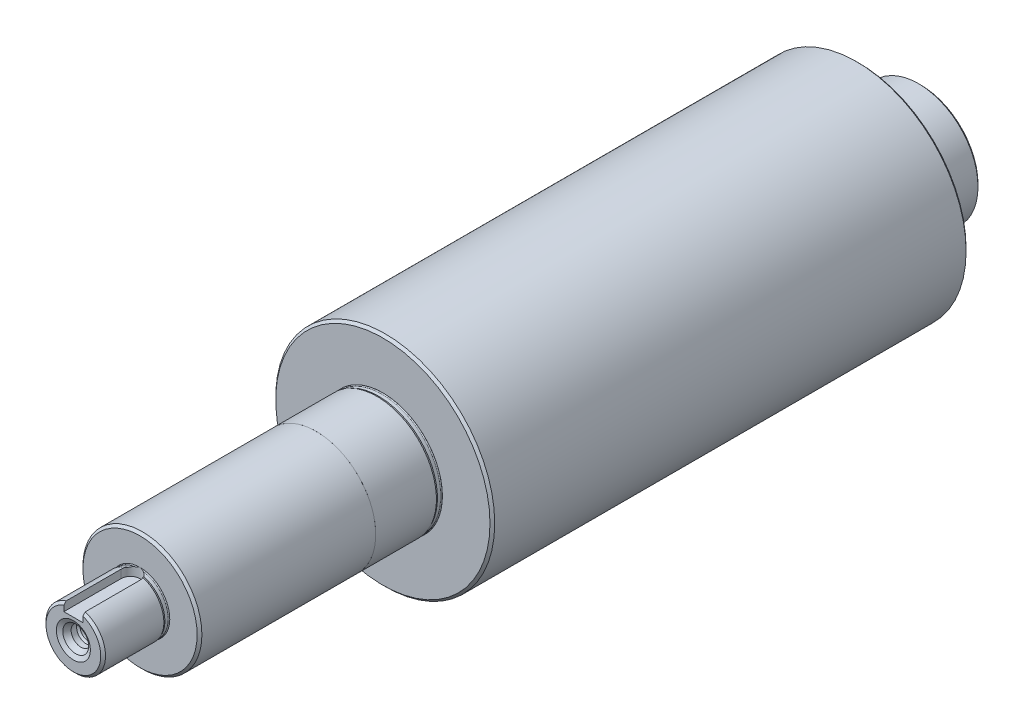
SolidWorks part; units mm, degrees
ref_plane "Přední rovina" through (0, 0, 0) normal (0, 0, 1) x (1, 0, 0)
ref_plane "Horní rovina" through (0, 0, 0) normal (0, 1, 0) x (1, 0, 0)
ref_plane "Pravá rovina" through (0, 0, 0) normal (1, 0, 0) x (0, 0, -1)
sketch "Skica1" plane through (0, 0, 0) normal (0, 0, 1) x (1, 0, 0)
  circle A0 centre (0, 0) radius 25
  dimension "D1" = 50
extrude "Přidat vysunutím1" add sketch "Skica1" along normal blind 26
sketch "Skica2" plane through (0, 0, 26) normal (0, 0, 1) x (1, 0, 0)
  circle A0 centre (0, 0) radius 46
  dimension "D1" = 92
extrude "Přidat vysunutím2" add sketch "Skica2" along normal blind 200
sketch "Skica3" plane through (0, 0, 226) normal (0, 0, 1) x (1, 0, 0)
  circle A0 centre (0, 0) radius 25
  dimension "D1" = 50
extrude "Přidat vysunutím3" add sketch "Skica3" along normal blind 28
sketch "Skica4" plane through (0, 0, 254) normal (0, 0, 1) x (1, 0, 0)
  circle A0 centre (0, 0) radius 24.99
  dimension "D1" = 49.98
extrude "Přidat vysunutím4" add sketch "Skica4" along normal blind 74
sketch "Skica5" plane through (0, 0, 328) normal (0, 0, 1) x (1, 0, 0)
  circle A0 centre (0, 0) radius 12.5
  dimension "D1" = 25
extrude "Přidat vysunutím5" add sketch "Skica5" along normal blind 28
chamfer "Zkosení1" distance 1 angle 45 5 edges at (25, 0, 0) (46, 0, 26) (46, 0, 226) (24.99, 0, 328) (12.5, 0, 356)
sketch "Skica15" plane through (0, 0, 0) normal (1, 0, 0) x (0, 0, -1)
  line L0 (-226.4, 24.7) -> (-227.7757, 24.7)
  line L1 (-227.7757, 24.7) -> (-228.5, 25)
  line L2 (-226, 25) -> (-254, 25) construction
  line L3 (-228.5, 25) -> (-226.0127, 25)
  line L4 (-226, 45) -> (-226, -45) construction
  line L5 (-23.5127, 25) -> (-24.2863, 24.8734)
  line L6 (-1, 25) -> (-26, 25) construction
  line L7 (-400.4428, 0) -> (-453.0486, 0) construction
  line L8 (-24.2863, 24.8734) -> (-25.6621, 24.8734)
  line L9 (-23.5127, 25) -> (-26, 25)
  line L10 (-26, -25) -> (-26, 25) construction
  line L11 (-26, -45) -> (-26, 45) construction
  line L12 (-328, 12.5) -> (-330.4873, 12.5)
  line L13 (-328, 12.5) -> (-355, 12.5) construction
  line L14 (-330.4873, 12.5) -> (-329.763, 12.2)
  line L15 (-329.763, 12.2) -> (-328.3873, 12.2)
  arc A0 (-226.4, 24.7) -> (-226.0127, 25) centre (-226.4, 25.1) ccw
  arc A1 (-25.6621, 24.8734) -> (-26, 25) centre (-25.7058, 25.271) cw
  arc A2 (-328.3873, 12.2) -> (-328, 12.5) centre (-328.3873, 12.6) ccw
  dimension "D3" = 0.8
  dimension "D1" = 0.3
  dimension "D2" = 2.5
  dimension "D4" = 2.4873
  dimension "D5" = 22.5
  dimension "D6" = 0.3
revolve "Odebrat rotací12" cut sketch "Skica15" angle 360 about L7
sketch "Skica16" plane through (0, 0, 0) normal (0, 1, 0) x (1, 0, 0)
  line L0 (0, -359.2533) -> (0, -335.2533) construction
  line L1 (-4, -356) -> (-4, -332)
  line L2 (4, -356) -> (4, -332)
  line L4 (-11.5, -356) -> (11.5, -356) construction
  line L5 (-4, -356) -> (4, -356)
  line L6 (4, -356) -> (4, -332)
  line L7 (-23.99, -328) -> (23.99, -328) construction
  arc A0 (-4, -332) -> (4, -332) centre (0, -332) cw
  point P3 (0, -373)
  dimension "D4" = 4
  dimension "D1" = 8
  dimension "D3" = 4
extrude "Odebrat vysunutím2" cut sketch "Skica16" against normal blind 4.1 from offset 12.5
ref_plane "Rovina1" through (0, 0, 0) normal (0, 1, 0) x (1, 0, 0)
sketch "Skica17" plane through (0, 0, 0) normal (0, 1, 0) x (1, 0, 0)
  line L0 (0, -356) -> (0, -360.8417) construction
  line L1 (-11.5, -356) -> (11.5, -356) construction
  line L2 (0, -356) -> (-7.15, -356)
  line L3 (-7.15, -356) -> (-5.4179, -355)
  line L4 (-5.4179, -355) -> (-4.1478, -352.8)
  line L5 (-4.1478, -352.8) -> (-4.1478, -350.5)
  line L7 (0, -356) -> (0, -349.7522)
  line L8 (-4.1478, -350.5) -> (-3.4, -349.7522)
  line L9 (-3.4, -349.7522) -> (0, -349.7522)
  dimension "D1" = 60
  dimension "D2" = 1
  dimension "D3" = 2.2
  dimension "D4" = 5.5
  dimension "D5" = 30
  dimension "D6" = 45
  dimension "D7" = 7.15
  dimension "D8" = 3.4
revolve "Odebrat rotací14" cut sketch "Skica17" angle 360 about L0
hole_wizard "M8 závit1" positions "Skica19" profile "Skica18" tap size "M8" standard "DIN"
sketch "Skica19" plane through (0, 0, 349.7522) normal (0, 0, 1) x (1, 0, 0)
  point P0 (0, 0)
sketch "Skica18" plane through (0, 0, 349.7522) normal (1, 0, 0) x (0, -1, 0)
  line L0 (0, 0) -> (0, 27.0429)
  line L1 (0, 27.0429) -> (3.4, 25)
  line L2 (3.4, 25) -> (3.4, 0)
  line L5 (3.4, 0) -> (0, 0)
  line L10 (0, 27.0429) -> (-3.4, 25) construction
  line L11 (0, -6.35) -> (0, 107.95) construction
  dimension "Průměr závitníku" = 6.8
  dimension "Hloubka závitníku" = 25
  dimension "Úhel vrtání" = 118
cosmetic thread "Závit díry1" parameters "D1"=23.75, "D2"=8
